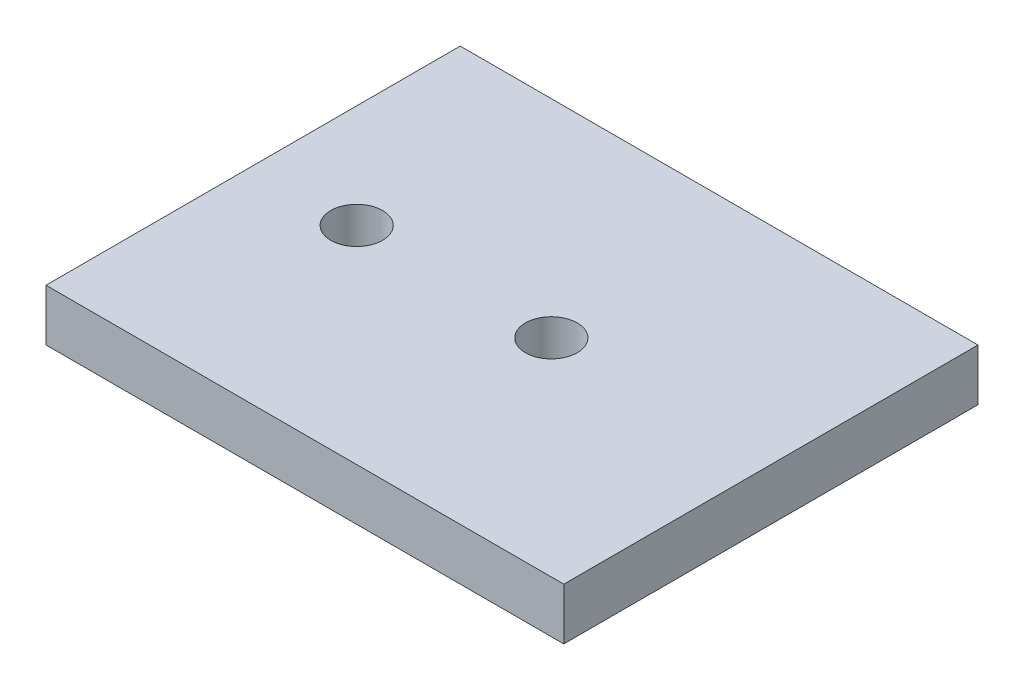
SolidWorks part; units mm, degrees
material "ABS"
ref_plane "Front Plane" through (0, 0, 0) normal (0, 0, 1) x (1, 0, 0)
ref_plane "Top Plane" through (0, 0, 0) normal (0, 1, 0) x (1, 0, 0)
ref_plane "Right Plane" through (0, 0, 0) normal (1, 0, 0) x (0, 0, -1)
sketch "Sketch1" plane through (0, 0, 0) normal (0, 1, 0) x (1, 0, 0)
  line L1 (-63.5, 50.8) -> (63.5, 50.8)
  line L2 (-63.5, 50.8) -> (-63.5, -50.8)
  line L3 (-63.5, -50.8) -> (63.5, -50.8)
  line L4 (63.5, 50.8) -> (63.5, -50.8)
  line L5 (-63.5, 50.8) -> (63.5, -50.8) construction
  line L6 (-63.5, -50.8) -> (63.5, 50.8) construction
  point P0 (0, 0)
  dimension "D1" = 127
  dimension "D2" = 101.6
extrude "Boss-Extrude1" add sketch "Sketch1" along normal blind 12.7
sketch "Sketch2" plane through (0, 12.7, 0) normal (0, 1, 0) x (1, 0, 0)
  line L1 (-63.5, 50.8) -> (-63.5, -50.8) construction
  line L2 (-63.5, 0) -> (63.5, 0) construction
  line L3 (63.5, -50.8) -> (63.5, 50.8) construction
  circle A0 centre (-38.1, 0) radius 6.35
  circle A1 centre (9.652, 0) radius 6.35
  dimension "D1" = 12.7
  dimension "D2" = 25.4
  dimension "D3" = 47.752
extrude "Cut-Extrude1" cut sketch "Sketch2" against normal through all
